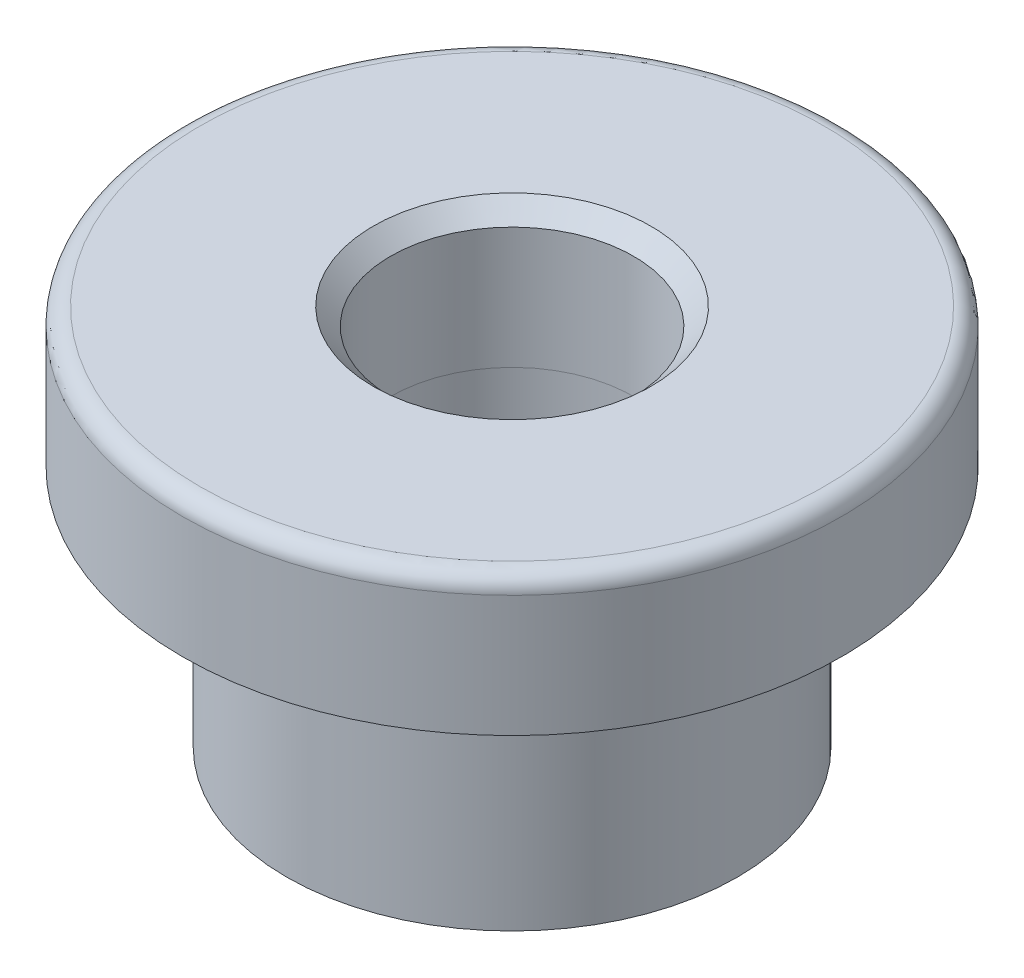
SolidWorks part; units mm, degrees
material "Aluminum Bronze"
ref_plane "Front Plane" through (0, 0, 0) normal (0, 0, 1) x (1, 0, 0)
ref_plane "Top Plane" through (0, 0, 0) normal (0, 1, 0) x (1, 0, 0)
ref_plane "Right Plane" through (0, 0, 0) normal (1, 0, 0) x (0, 0, -1)
sketch "Sketch1" plane through (0, 0, 0) normal (0, 1, 0) x (1, 0, 0)
  circle A0 centre (0, 0) radius 6.5
  circle A1 centre (0, 0) radius 3.5
extrude "Boss-Extrude1" add sketch "Sketch1" along normal blind 7
sketch "Sketch2" plane through (0, 7, 0) normal (0, 1, 0) x (1, 0, 0)
  circle A0 centre (0, 0) radius 9.5
  circle A1 centre (0, 0) radius 3.5032
extrude "Boss-Extrude3" add sketch "Sketch2" along normal blind 4
chamfer "Chamfer1" distance 0.5 angle 45 1 edges at (0, 11, 3.5032)
fillet "Fillet1" radius 0.5 1 edges at (0, 11, 9.5)
